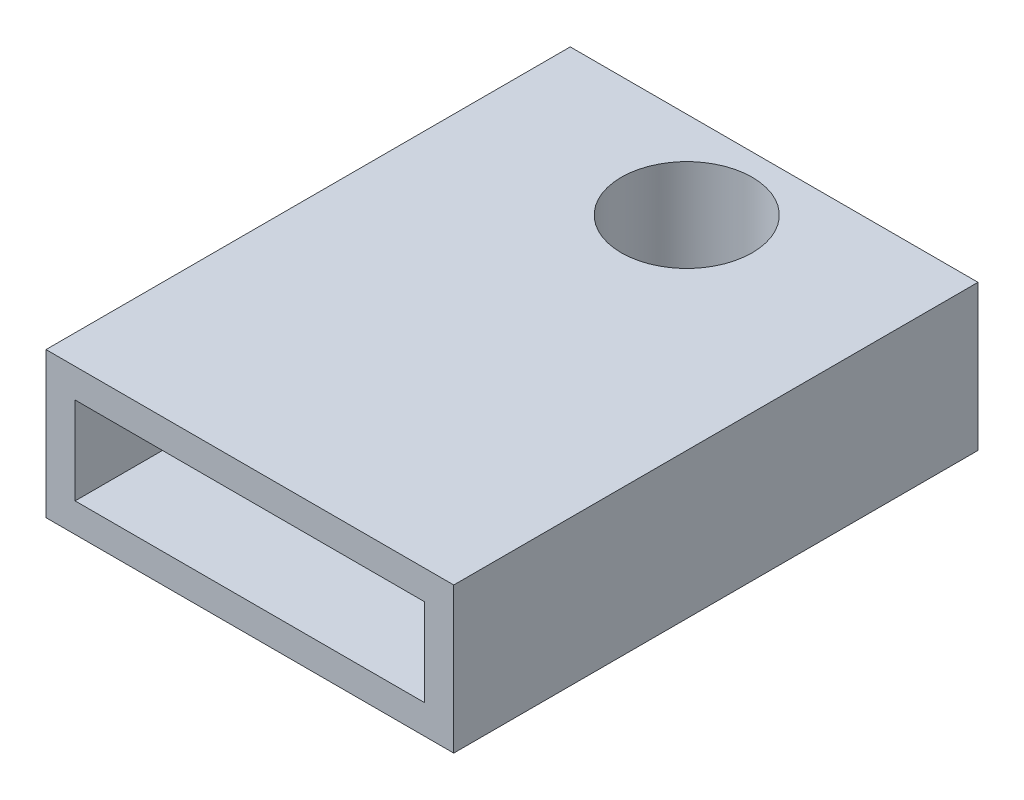
SolidWorks part; units mm, degrees
ref_plane "Front Plane" through (0, 0, 0) normal (0, 0, 1) x (1, 0, 0)
ref_plane "Top Plane" through (0, 0, 0) normal (0, 1, 0) x (1, 0, 0)
ref_plane "Right Plane" through (0, 0, 0) normal (1, 0, 0) x (0, 0, -1)
sketch "Sketch1" plane through (0, 0, 0) normal (0, 0, 1) x (1, 0, 0)
  line L1 (-4.0462, 1.9118) -> (9.9538, 1.9118)
  line L2 (-4.0462, 1.9118) -> (-4.0462, -3.0882)
  line L3 (-4.0462, -3.0882) -> (9.9538, -3.0882)
  line L4 (9.9538, 1.9118) -> (9.9538, -3.0882)
  dimension "D1" = 5
  dimension "D2" = 14
extrude "Boss-Extrude1" add sketch "Sketch1" against normal blind 18
sketch "Sketch2" plane through (0, 0, 0) normal (0, 0, 1) x (1, 0, 0)
  line L0 (-4.0462, 1.9118) -> (-4.0462, -3.0882) construction
  line L1 (-3.0462, 0.9118) -> (8.9538, 0.9118)
  line L2 (-3.0462, 0.9118) -> (-3.0462, -2.0882)
  line L3 (-3.0462, -2.0882) -> (8.9538, -2.0882)
  line L4 (8.9538, 0.9118) -> (8.9538, -2.0882)
  line L5 (9.9538, -3.0882) -> (9.9538, 1.9118) construction
  line L6 (-4.0462, -3.0882) -> (9.9538, -3.0882) construction
  line L7 (9.9538, 1.9118) -> (-4.0462, 1.9118) construction
  dimension "D1" = 1
  dimension "D2" = 1
  dimension "D3" = 1
  dimension "D4" = 1
extrude "Cut-Extrude1" cut sketch "Sketch2" against normal blind 8
hole_wizard "#8 Clearance Hole1" positions "3DSketch1" profile "Sketch3" hole size "#8" standard "ANSI Inch"
sketch3d "3DSketch1"
  line L0 (-4.0462, -3.0882, -18) -> (9.9538, -3.0882, -18) construction
  line L1 (-4.0462, -3.0882, -18) -> (-4.0462, -3.0882, 0) construction
  point P0 (2.9538, -3.0882, -15)
  dimension "D1" = 3
  dimension "D2" = 7
sketch "Sketch3" plane through (2.9538, -3.0882, -15) normal (1, 0, 0) x (0, 0, -1)
  line L0 (0, 0) -> (0, 18.3507)
  line L1 (0, 18.3507) -> (2.2479, 17)
  line L2 (2.2479, 17) -> (2.2479, 0)
  line L5 (2.2479, 0) -> (0, 0)
  line L10 (0, 18.3507) -> (-2.2479, 17) construction
  line L11 (0, -6.35) -> (0, 107.95) construction
  dimension "Hole Dia." = 4.4958
  dimension "Hole Depth" = 17
  dimension "Drill Angle" = 118
